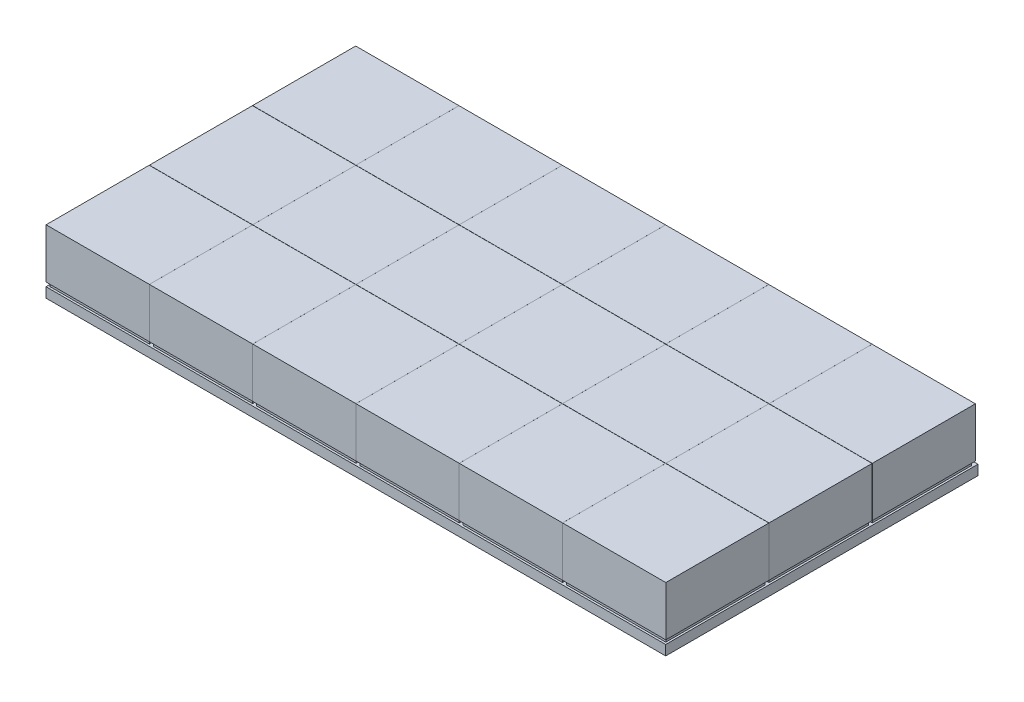
SolidWorks part; units mm, degrees
ref_plane "Front Plane" through (0, 0, 0) normal (0, 0, 1) x (1, 0, 0)
ref_plane "Top Plane" through (0, 0, 0) normal (0, 1, 0) x (1, 0, 0)
ref_plane "Right Plane" through (0, 0, 0) normal (1, 0, 0) x (0, 0, -1)
sketch "Sketch1" plane through (0, 0, 0) normal (0, 1, 0) x (1, 0, 0)
  line L1 (-240, -135) -> (240, -135)
  line L2 (-240, -135) -> (-240, 135)
  line L3 (-240, 135) -> (240, 135)
  line L4 (240, -135) -> (240, 135)
  line L5 (-240, -135) -> (240, 135) construction
  line L6 (-240, 135) -> (240, -135) construction
  point P0 (0, 0)
  dimension "D1" = 480
  dimension "D2" = 270
extrude "Boss-Extrude1" add sketch "Sketch1" along normal blind 5
sketch "Sketch2" plane through (0, 5, 0) normal (0, 1, 0) x (1, 0, 0)
  line L0 (0, 0) -> (0, -135) construction
  line L1 (-240, -135) -> (240, -135) construction
  line L3 (-25, -80) -> (25, -80)
  line L4 (-25, -80) -> (-25, -130)
  line L5 (-25, -130) -> (25, -130)
  line L6 (25, -80) -> (25, -130)
  line L7 (-25, -80) -> (25, -130) construction
  line L8 (-25, -130) -> (25, -80) construction
  point P5 (0, -105)
  dimension "D1" = 50
  dimension "D2" = 50
  dimension "D3" = 5
extrude "Boss-Extrude3" add sketch "Sketch2" along normal blind 2
pattern_linear "LPattern1" count 5 spacing 52 along (0, 0, -1) of "Boss-Extrude3"
sketch "Sketch3" plane through (0, 7, 0) normal (0, 1, 0) x (1, 0, 0)
  line L0 (0, 0) -> (0, -130) construction
  line L1 (-25, -130) -> (25, -130) construction
  line L3 (-26, -79.1) -> (26, -79.1)
  line L4 (-26, -79.1) -> (-26, -131)
  line L5 (-26, -131) -> (26, -131)
  line L6 (26, -79.1) -> (26, -131)
  line L7 (-26, -79.1) -> (26, -131) construction
  line L8 (-26, -131) -> (26, -79.1) construction
  line L9 (-240, -135) -> (240, -135) construction
  point P5 (0, -105.05)
  dimension "D1" = 52
  dimension "D2" = 51.9
  dimension "D3" = 4
extrude "Boss-Extrude8" add sketch "Sketch3" along normal blind 25
pattern_linear "LPattern5" count 5 spacing 52 along (0, 0, -1) of "Boss-Extrude8"
pattern_linear "LPattern6" count 4 spacing 52.01 along (1, 0, 0) count 5 spacing 52.01 along (-1, 0, 0) of "Boss-Extrude3", "LPattern1", "Boss-Extrude8", "LPattern5"
sketch "Sketch4" plane through (0, 5, 0) normal (0, 1, 0) x (1, 0, 0)
  line L0 (240, 135) -> (-240, 135) construction
  line L17 (-182.0341, 135) -> (-240, 135)
  line L18 (-182.0341, 135) -> (-182.0341, -135)
  line L19 (-182.0341, -135) -> (-240, -135)
  line L20 (-240, 135) -> (-240, -135)
  line L21 (130.0253, 135.5507) -> (240, 135.5507)
  line L22 (130.0253, 135.5507) -> (130.0253, -135)
  line L23 (130.0253, -135) -> (240, -135)
  line L24 (240, 135.5507) -> (240, -135)
  point P4 (-181.03, 135)
  point P12 (-182.0463, 135)
  point P13 (0, 0)
  point P19 (0, 0)
  point P22 (0, 0)
extrude "Cut-Extrude1" cut sketch "Sketch4" against normal through all both and the other way through all
sketch "Sketch5" plane through (0, 5, 0) normal (0, 1, 0) x (1, 0, 0)
  line L0 (-182.0341, 135) -> (-182.0341, -135) construction
  line L1 (-182.0341, -27.0515) -> (130.0253, -27.0515)
  line L2 (-182.0341, -27.0515) -> (-182.0341, -135)
  line L3 (-182.0341, -135) -> (130.0253, -135)
  line L4 (130.0253, -27.0515) -> (130.0253, -135)
  line L11 (-182.0345, 135) -> (130.0253, 135)
  line L12 (-182.0345, 135) -> (-182.0345, 130.2098)
  line L13 (-182.0345, 130.2098) -> (130.0253, 130.2098)
  line L14 (130.0253, 135) -> (130.0253, 130.2098)
  point P7 (0, 0)
extrude "Cut-Extrude2" cut sketch "Sketch5" against normal through all both and the other way through all
